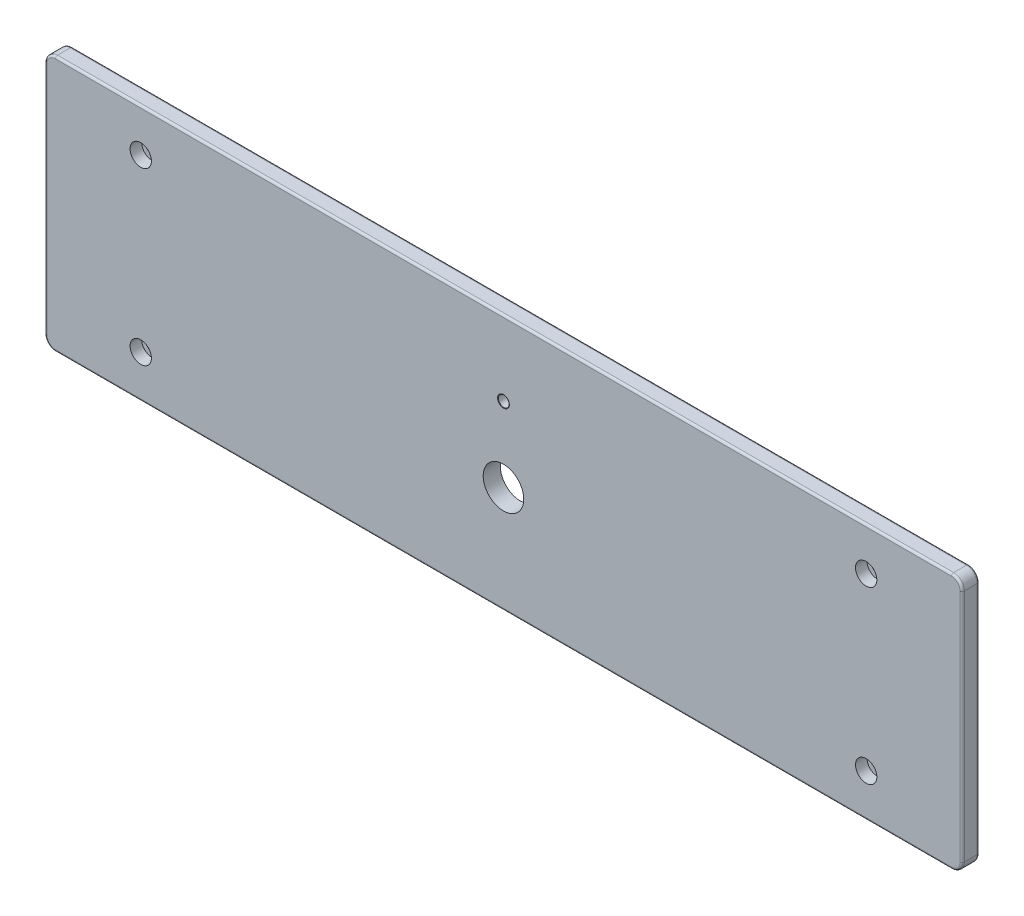
SolidWorks part; units mm, degrees
material "7079 Alloy"
ref_plane "Front Plane" through (0, 0, 0) normal (0, 0, 1) x (1, 0, 0)
ref_plane "Top Plane" through (0, 0, 0) normal (0, 1, 0) x (1, 0, 0)
ref_plane "Right Plane" through (0, 0, 0) normal (1, 0, 0) x (0, 0, -1)
sketch "Sketch1" plane through (0, 0, 0) normal (0, 0, 1) x (1, 0, 0)
  line L1 (0, 0) -> (430, 0)
  line L2 (0, 0) -> (0, 120)
  line L3 (0, 120) -> (430, 120)
  line L4 (430, 0) -> (430, 120)
extrude "Extrude1" add sketch "Sketch1" along normal blind 8
fillet "Fillet1" radius 5 4 edges at (0, 0, 4) (430, 0, 4) (430, 120, 4) (0, 120, 4)
fillet "Fillet2" radius 1 16 edges at (428.5355, 1.4645, 0) (1.4645, 118.5355, 0) (0, 60, 0) (1.4645, 1.4645, 0) (215, 0, 0) (428.5355, 118.5355, 0) (430, 60, 0) (1.4645, 118.5355, 8) (428.5355, 118.5355, 8) (430, 60, 8) (428.5355, 1.4645, 8) (215, 0, 8) (1.4645, 1.4645, 8) (0, 60, 8) (215, 120, 0) (215, 120, 8)
sketch "Sketch2" plane through (0, 0, 8) normal (0, 0, 1) x (1, 0, 0)
  line L0 (45, 20) -> (45, 100) construction
  line L1 (45, 100) -> (385, 100) construction
  line L2 (385, 100) -> (385, 20) construction
  line L3 (385, 20) -> (45, 20) construction
  line L4 (215, 20) -> (215, 50) construction
  line L5 (215, 50) -> (215, 85) construction
  line L6 (215, 85) -> (215, 100) construction
hole_wizard "CBORE for M5 Hex Socket Head Cap Screw1" positions "3DSketch1" profile "Sketch3" counterbore size "M5" standard "DIN" end condition through all
sketch3d "3DSketch1"
  point P0 (45, 100, 8)
  point P3 (45, 20, 8)
  point P6 (385, 20, 8)
  point P9 (385, 100, 8)
sketch "Sketch3" plane through (45, 100, 8) normal (1, 0, 0) x (0, -1, 0)
  line L0 (0, 0) -> (0, 8)
  line L1 (0, 8) -> (2.75, 8)
  line L3 (2.75, 8) -> (2.75, 5.4)
  line L4 (2.75, 5.4) -> (5, 5.4)
  line L5 (5, 5.4) -> (5, 0)
  line L7 (5, 0) -> (0, 0)
  line L11 (0, -6.35) -> (0, 107.95) construction
  dimension "Thru Hole Dia." = 5.5
  dimension "Thru Hole Depth" = 8
  dimension "C'Bore Dia." = 10
  dimension "C'Bore Depth" = 5.4
hole_wizard "Ø5.0 (5) Diameter Hole1" positions "3DSketch2" profile "Sketch5" hole size "Ø5.0" standard "DIN" end condition through all
sketch3d "3DSketch2"
  point P0 (215, 85, 8)
sketch "Sketch5" plane through (215, 85, 8) normal (1, 0, 0) x (0, -1, 0)
  line L0 (0, 0) -> (0, 8)
  line L1 (0, 8) -> (2.5, 8)
  line L2 (2.5, 8) -> (2.5, 0)
  line L5 (2.5, 0) -> (0, 0)
  line L11 (0, -6.35) -> (0, 107.95) construction
  dimension "Thru Hole Dia." = 5
  dimension "Thru Hole Depth" = 8
hole_wizard "Ø19.0 (19) Diameter Hole1" positions "3DSketch3" profile "Sketch6" hole size "Ø19.0" standard "DIN" end condition through all
sketch3d "3DSketch3"
  point P0 (215, 50, 8)
sketch "Sketch6" plane through (215, 50, 8) normal (1, 0, 0) x (0, -1, 0)
  line L0 (0, 0) -> (0, 8)
  line L1 (0, 8) -> (9.5, 8)
  line L2 (9.5, 8) -> (9.5, 0)
  line L5 (9.5, 0) -> (0, 0)
  line L11 (0, -6.35) -> (0, 107.95) construction
  dimension "Thru Hole Dia." = 19
  dimension "Thru Hole Depth" = 8
chamfer "Chamfer1" distance 0.25 angle 30 1 edges at (217.5, 85, 8)
